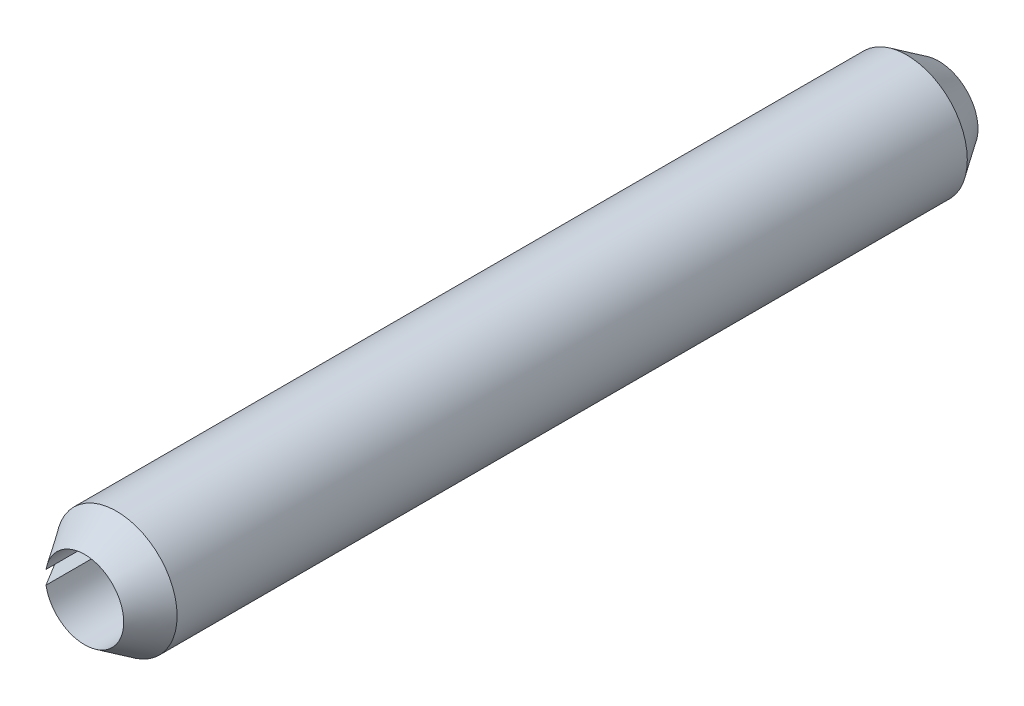
SolidWorks part; units mm, degrees
material "AISI 1045 Steel, cold drawn"
ref_plane "Front Plane" through (0, 0, 0) normal (0, 0, 1) x (1, 0, 0)
ref_plane "Top Plane" through (0, 0, 0) normal (0, 1, 0) x (1, 0, 0)
ref_plane "Right Plane" through (0, 0, 0) normal (1, 0, 0) x (0, 0, -1)
sketch "Sketch1" plane through (0, 0, 0) normal (0, 0, 1) x (1, 0, 0)
  line L0 (0.55, 0) -> (0.85, 0) construction
  line L1 (-0.8371, 0.1476) -> (-0.5416, 0.0955)
  line L2 (-0.5416, -0.0955) -> (-0.8371, -0.1476)
  arc A0 (-0.8371, -0.1476) -> (-0.8371, 0.1476) centre (0, 0) ccw
  arc A1 (-0.5416, -0.0955) -> (-0.5416, 0.0955) centre (0, 0) ccw
  dimension "OD" = 1.7
  dimension "Wall thickness" = 0.3
  dimension "D3" = 20
extrude "Extrude1" add sketch "Sketch1" along normal mid plane 12
sketch "Sketch2" plane through (0, 0, 0) normal (1, 0, 0) x (0, 0, -1)
  line L0 (0, -0.85) -> (0, 0.85) construction
  line L1 (6, 0) -> (-6, 0) construction
  line L2 (6, -0.55) -> (6, 0.55) construction
  line L3 (6, 0.85) -> (-6, 0.85) construction
  line L4 (6, 0.85) -> (6, 0.55)
  line L5 (6, 0.55) -> (5.55, 0.85)
  line L6 (5.55, 0.85) -> (6, 0.85)
  line L7 (6, -0.85) -> (6, 0.85) construction
  line L8 (-5.55, 0.85) -> (-6, 0.85)
  line L9 (-6, 0.55) -> (-5.55, 0.85)
  line L10 (-6, 0.85) -> (-6, 0.55)
  line L11 (5.55, -0.85) -> (6, -0.85) construction
  line L12 (6, -0.55) -> (5.55, -0.85) construction
  line L13 (6, -0.85) -> (6, -0.55) construction
  dimension "B" = 1.1
  dimension "Chamfer max" = 0.45
revolve "Cut-Revolve1" cut sketch "Sketch2" angle 360 about L1
sketch "Sketch3" plane through (0, 0, 0) normal (0, 0, 1) x (1, 0, 0)
  line L0 (0.55, 0) -> (0.85, 0) construction
  line L1 (0.55, 0) -> (0.85, 0)
  circle A0 centre (0, 0) radius 0.85
  circle A1 centre (0, 0) radius 0.55
  arc A2 (-0.8371, -0.1476) -> (-0.8371, 0.1476) centre (0, 0) ccw construction
  arc A3 (-0.5416, -0.0955) -> (-0.5416, 0.0955) centre (0, 0) ccw construction
